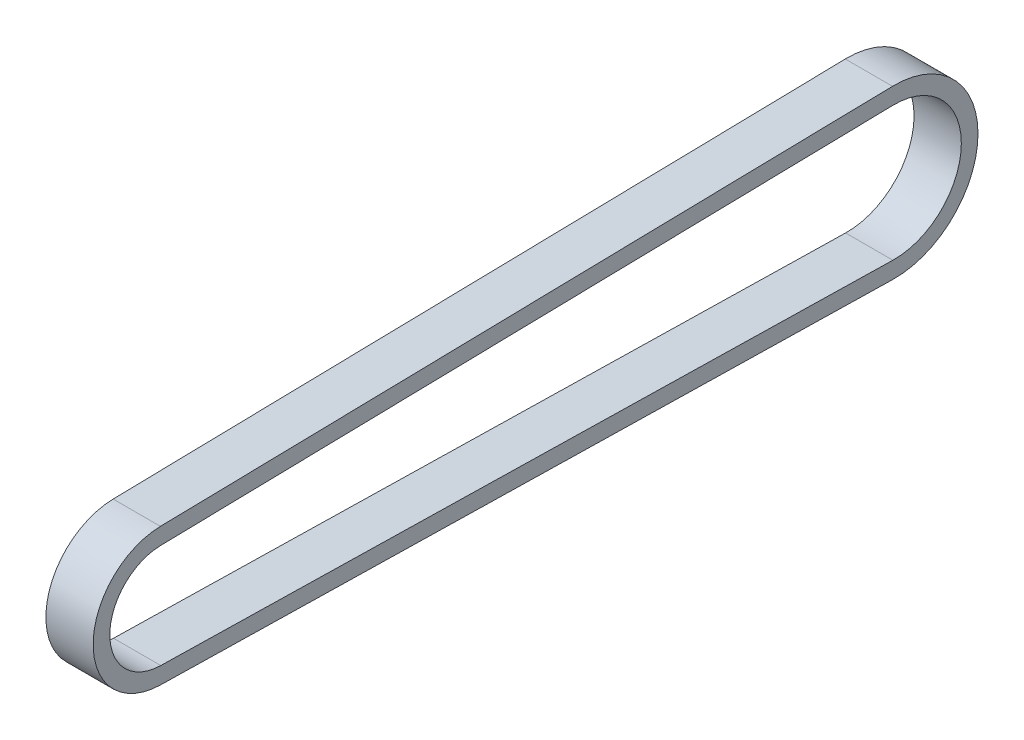
SolidWorks part; units mm, degrees
ref_plane "Front Plane" through (0, 0, 0) normal (0, 0, 1) x (1, 0, 0)
ref_plane "Top Plane" through (0, 0, 0) normal (0, 1, 0) x (1, 0, 0)
ref_plane "Right Plane" through (0, 0, 0) normal (1, 0, 0) x (0, 0, -1)
other "Bounding Box"
ref_plane "Default Plane" through (-8.9266, -12.7485, 0) normal (-0.1736, 0.9848, 0) x (0.9848, 0.1736, 0)
sketch "Sketch1" plane through (0, 0, 0) normal (1, 0, 0) x (0, 0, -1)
  line L0 (0, 0) -> (139.4714, 0) construction
  line L1 (-0.2035, 9.9064) -> (139.209, 12.771)
  line L2 (-0.2035, -9.9064) -> (139.209, -12.771)
  line L3 (-0.2688, 13.0808) -> (139.1438, 15.9453)
  line L4 (-0.2688, -13.0808) -> (139.1438, -15.9453)
  line L5 (-9.9085, 0) -> (-13.0835, 0) construction
  line L6 (152.2451, 0) -> (155.4201, 0) construction
  arc A0 (-0.2035, 9.9064) -> (-0.2035, -9.9064) centre (0, 0) ccw
  arc A1 (139.209, -12.771) -> (139.209, 12.771) centre (139.4714, 0) ccw
  arc A2 (-0.2688, 13.0808) -> (-0.2688, -13.0808) centre (0, 0) ccw
  arc A3 (139.1438, -15.9453) -> (139.1438, 15.9453) centre (139.4714, 0) ccw
  dimension "D2" = 3.175
  dimension "D4" = 19.8171
  dimension "D5" = 25.5473
  dimension "D1" = 139.4714
extrude "Boss-Extrude1" add sketch "Sketch1" along normal mid plane 9
